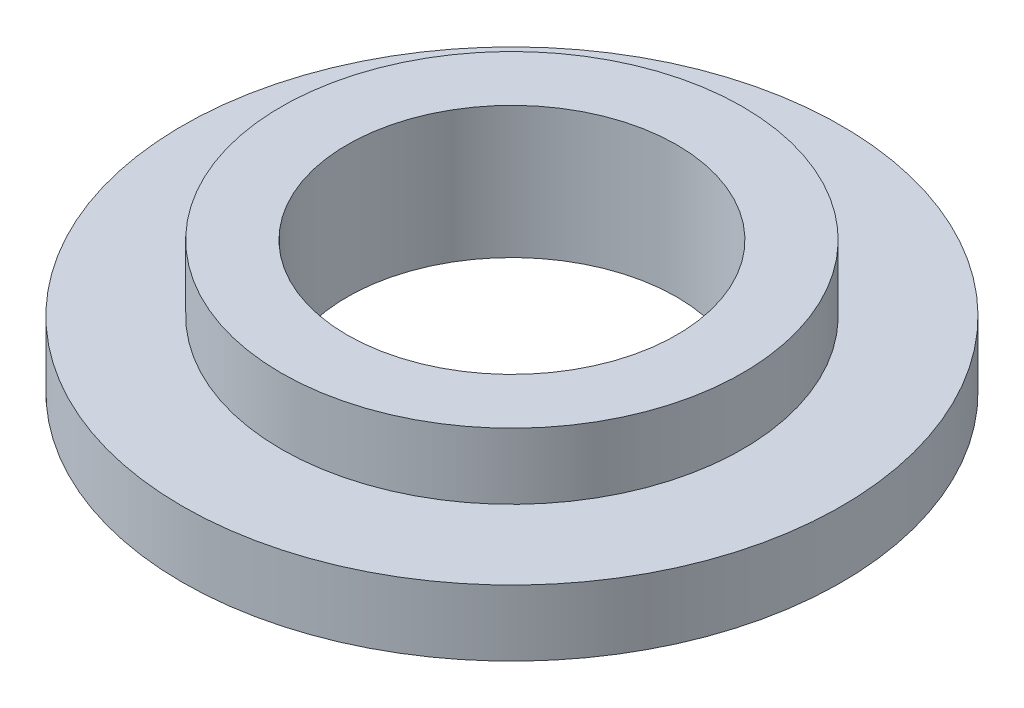
SolidWorks part; units mm, degrees
material "Простая углеродистая сталь"
ref_plane "Спереди" through (0, 0, 0) normal (0, 0, 1) x (1, 0, 0)
ref_plane "Сверху" through (0, 0, 0) normal (0, 1, 0) x (1, 0, 0)
ref_plane "Справа" through (0, 0, 0) normal (1, 0, 0) x (0, 0, -1)
sketch "Эскиз1" plane through (0, 0, 0) normal (1, 0, 0) x (0, 0, -1)
  line L0 (25, 0) -> (50, 0)
  line L1 (50, 0) -> (50, 10)
  line L2 (50, 10) -> (35, 10)
  line L3 (35, 10) -> (35, 20)
  line L4 (35, 20) -> (25, 20)
  line L5 (25, 20) -> (25, 0)
  line L6 (0, 30.7841) -> (0, -19.0919) construction
  dimension "D1" = 25
  dimension "D2" = 25
  dimension "D3" = 10
  dimension "D4" = 20
  dimension "D5" = 15
revolve "Повернуть1" add sketch "Эскиз1" angle 360 about L6
